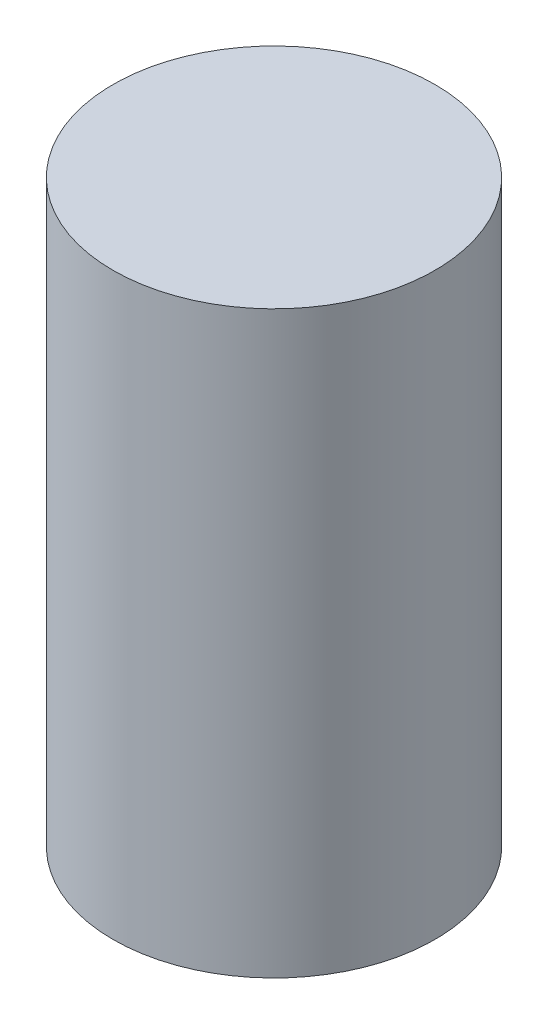
SolidWorks part; units mm, degrees
ref_plane "Front Plane" through (0, 0, 0) normal (0, 0, 1) x (1, 0, 0)
ref_plane "Top Plane" through (0, 0, 0) normal (0, 1, 0) x (1, 0, 0)
ref_plane "Right Plane" through (0, 0, 0) normal (1, 0, 0) x (0, 0, -1)
sketch "Sketch1" plane through (0, 0, 0) normal (0, 1, 0) x (1, 0, 0)
  circle A0 centre (0, 0) radius 1.25
  dimension "D1" = 2.5
extrude "Boss-Extrude1" add sketch "Sketch1" along normal blind 4.5
